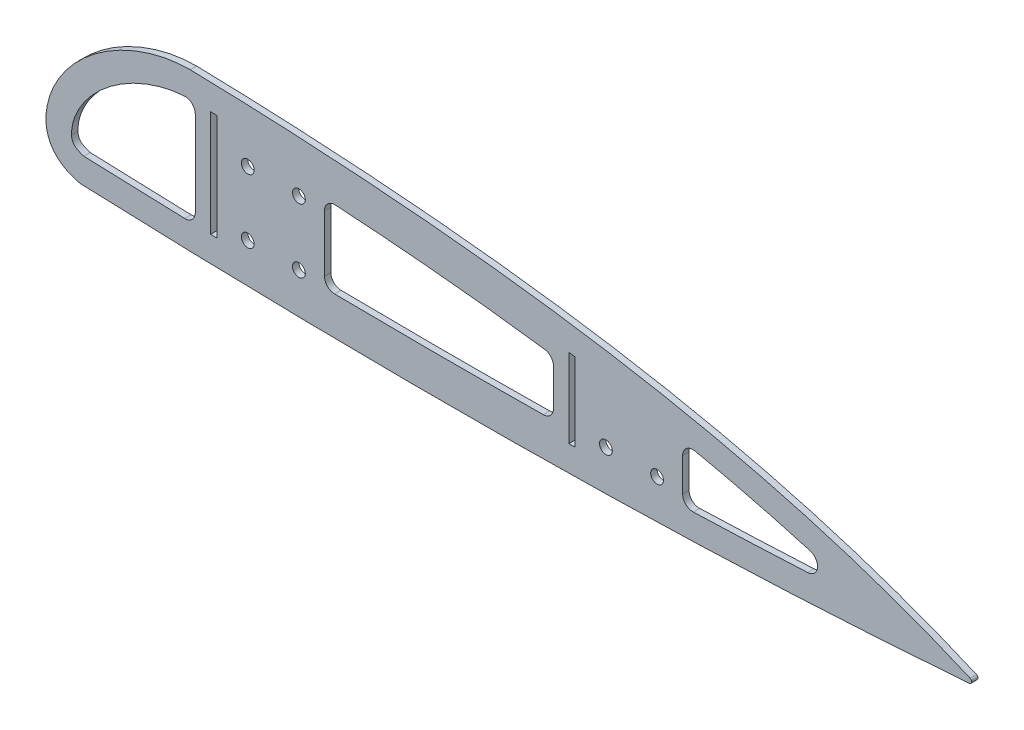
SolidWorks part; units mm, degrees
material "Balsa"
ref_plane "Front Plane" through (0, 0, 0) normal (0, 0, 1) x (1, 0, 0)
ref_plane "Top Plane" through (0, 0, 0) normal (0, 1, 0) x (1, 0, 0)
ref_plane "Right Plane" through (0, 0, 0) normal (1, 0, 0) x (0, 0, -1)
sketch "Sketch1" plane through (0, 0, 0) normal (0, 0, 1) x (1, 0, 0)
  line L0 (0, 0) -> (0, 277.8723) construction
  spline S0 degree 3 poles (-1817.1035, 43.2459) (-1814.9934, 43.2498) (-1812.9023, 43.1407) (-1808.752, 42.7311) (-1806.6929, 42.4302) (-1802.6035, 41.6561) (-1800.5732, 41.1827) (-1797.5481, 40.3507) (-1796.5432, 40.0529) (-1794.54, 39.4173) (-1793.5437, 39.0799) (-1788.6128, 37.3067) (-1784.805, 35.6079) (-1779.2882, 32.661) (-1777.4821, 31.6116) (-1774.8234, 29.9338) (-1773.9447, 29.3566) (-1772.2094, 28.1699) (-1771.3541, 27.5612) (-1768.8255, 25.689) (-1767.1896, 24.3793) (-1764.8142, 22.3175) (-1764.0355, 21.6139) (-1762.5056, 20.173) (-1761.7542, 19.4353) (-1759.5596, 17.1863) (-1758.1698, 15.6335) (-1755.5473, 12.4134) (-1754.3146, 10.7461) (-1752.0262, 7.2824) (-1750.9703, 5.4862) (-1749.5454, 2.676) (-1749.0957, 1.7161) (-1748.267, -0.2215) (-1747.8871, -1.2004) (-1746.8587, -4.1696) (-1746.3198, -6.1918) (-1745.7821, -9.3043) (-1745.6482, -10.3589) (-1745.4865, -12.47) (-1745.458, -13.528) (-1745.4874, -14.5886) knots 0 0 0 0 0.0625 0.0625 0.125 0.125 0.1875 0.1875 0.21875 0.21875 0.25 0.25 0.375 0.375 0.4375 0.4375 0.46875 0.46875 0.5 0.5 0.5625 0.5625 0.59375 0.59375 0.625 0.625 0.6875 0.6875 0.75 0.75 0.8125 0.8125 0.84375 0.84375 0.875 0.875 0.9375 0.9375 0.96875 0.96875 1 1 1 1
  spline S1 degree 3 poles (-1745.4874, -14.5886) (-1745.5191, -15.733) (-1745.6389, -16.8608) (-1745.9656, -18.5246) (-1746.0991, -19.0746) (-1746.4188, -20.1646) (-1746.6063, -20.7076) (-1747.2456, -22.2976) (-1747.7692, -23.2982) (-1748.699, -24.7111) (-1749.033, -25.1674) (-1749.7496, -26.0504) (-1750.1342, -26.479) (-1751.337, -27.6959) (-1752.2075, -28.4223) (-1753.6032, -29.4008) (-1754.0844, -29.7089) (-1755.0714, -30.2875) (-1755.573, -30.5556) (-1757.0993, -31.3032) (-1758.1455, -31.7263) (-1760.2858, -32.4471) (-1761.3799, -32.7445) (-1762.4949, -32.9869) knots 0 0 0 0 0.125 0.125 0.1875 0.1875 0.25 0.25 0.375 0.375 0.4375 0.4375 0.5 0.5 0.625 0.625 0.6875 0.6875 0.75 0.75 0.875 0.875 1 1 1 1
  spline S2 degree 3 poles (-1762.4949, -32.9869) (-1799.6912, -34.4623) (-1836.8983, -35.536) (-1892.7275, -36.4562) (-1911.3397, -36.6475) (-1948.5616, -36.7793) (-1967.1723, -36.72) (-2004.3932, -36.3278) (-2023.0051, -35.9948) (-2060.2115, -35.0301) (-2078.8075, -34.3983) (-2134.572, -32.0138) (-2171.7171, -29.7694) (-2208.8261, -26.7741) knots 0 0 0 0 0.25 0.25 0.375 0.375 0.5 0.5 0.625 0.625 0.75 0.75 1 1 1 1
  spline S3 degree 3 poles (-2208.8261, -26.7741) (-2193.5392, -19.9895) (-2178.0173, -13.8767) (-2146.5473, -2.869) (-2130.6, 2.0276) (-2110.436, 7.4917) (-2106.3936, 8.5512) (-2098.2976, 10.6045) (-2094.243, 11.5987) (-2082.06, 14.4883) (-2073.9125, 16.2908) (-2049.401, 21.3607) (-2032.9678, 24.2917) (-2008.204, 28.1331) (-1999.9354, 29.32) (-1983.39, 31.5219) (-1975.1103, 32.5374) (-1950.2526, 35.3512) (-1933.6558, 36.918) (-1900.4205, 39.5347) (-1883.7819, 40.5844) (-1850.4688, 42.2382) (-1833.7942, 42.8421) (-1817.1035, 43.2459) knots 0 0 0 0 0.125 0.125 0.25 0.25 0.28125 0.28125 0.3125 0.3125 0.375 0.375 0.5 0.5 0.5625 0.5625 0.625 0.625 0.75 0.75 0.875 0.875 1 1 1 1
  spline S4 degree 3 poles (2208.8261, -26.7741) (2193.5392, -19.9895) (2178.0173, -13.8767) (2146.5473, -2.869) (2130.6, 2.0276) (2110.436, 7.4917) (2106.3936, 8.5512) (2098.2976, 10.6045) (2094.243, 11.5987) (2082.06, 14.4883) (2073.9125, 16.2908) (2049.401, 21.3607) (2032.9678, 24.2917) (2008.204, 28.1331) (1999.9354, 29.32) (1983.39, 31.5219) (1975.1103, 32.5374) (1950.2526, 35.3512) (1933.6558, 36.918) (1900.4205, 39.5347) (1883.7819, 40.5844) (1850.4688, 42.2382) (1833.7942, 42.8421) (1817.1035, 43.2459) knots 0 0 0 0 0.125 0.125 0.25 0.25 0.28125 0.28125 0.3125 0.3125 0.375 0.375 0.5 0.5 0.5625 0.5625 0.625 0.625 0.75 0.75 0.875 0.875 1 1 1 1
  spline S5 degree 3 poles (1762.4949, -32.9869) (1799.6912, -34.4623) (1836.8983, -35.536) (1892.7275, -36.4562) (1911.3397, -36.6475) (1948.5616, -36.7793) (1967.1723, -36.72) (2004.3932, -36.3278) (2023.0051, -35.9948) (2060.2115, -35.0301) (2078.8075, -34.3983) (2134.572, -32.0138) (2171.7171, -29.7694) (2208.8261, -26.7741) knots 0 0 0 0 0.25 0.25 0.375 0.375 0.5 0.5 0.625 0.625 0.75 0.75 1 1 1 1
  spline S6 degree 3 poles (1745.4874, -14.5886) (1745.5191, -15.733) (1745.6389, -16.8608) (1745.9656, -18.5246) (1746.0991, -19.0746) (1746.4188, -20.1646) (1746.6063, -20.7076) (1747.2456, -22.2976) (1747.7692, -23.2982) (1748.699, -24.7111) (1749.033, -25.1674) (1749.7496, -26.0504) (1750.1342, -26.479) (1751.337, -27.6959) (1752.2075, -28.4223) (1753.6032, -29.4008) (1754.0844, -29.7089) (1755.0714, -30.2875) (1755.573, -30.5556) (1757.0993, -31.3032) (1758.1455, -31.7263) (1760.2858, -32.4471) (1761.3799, -32.7445) (1762.4949, -32.9869) knots 0 0 0 0 0.125 0.125 0.1875 0.1875 0.25 0.25 0.375 0.375 0.4375 0.4375 0.5 0.5 0.625 0.625 0.6875 0.6875 0.75 0.75 0.875 0.875 1 1 1 1
  spline S7 degree 3 poles (1817.1035, 43.2459) (1814.9934, 43.2498) (1812.9023, 43.1407) (1808.752, 42.7311) (1806.6929, 42.4302) (1802.6035, 41.6561) (1800.5732, 41.1827) (1797.5481, 40.3507) (1796.5432, 40.0529) (1794.54, 39.4173) (1793.5437, 39.0799) (1788.6128, 37.3067) (1784.805, 35.6079) (1779.2882, 32.661) (1777.4821, 31.6116) (1774.8234, 29.9338) (1773.9447, 29.3566) (1772.2094, 28.1699) (1771.3541, 27.5612) (1768.8255, 25.689) (1767.1896, 24.3793) (1764.8142, 22.3175) (1764.0355, 21.6139) (1762.5056, 20.173) (1761.7542, 19.4353) (1759.5596, 17.1863) (1758.1698, 15.6335) (1755.5473, 12.4134) (1754.3146, 10.7461) (1752.0262, 7.2824) (1750.9703, 5.4862) (1749.5454, 2.676) (1749.0957, 1.7161) (1748.267, -0.2215) (1747.8871, -1.2004) (1746.8587, -4.1696) (1746.3198, -6.1918) (1745.7821, -9.3043) (1745.6482, -10.3589) (1745.4865, -12.47) (1745.458, -13.528) (1745.4874, -14.5886) knots 0 0 0 0 0.0625 0.0625 0.125 0.125 0.1875 0.1875 0.21875 0.21875 0.25 0.25 0.375 0.375 0.4375 0.4375 0.46875 0.46875 0.5 0.5 0.5625 0.5625 0.59375 0.59375 0.625 0.625 0.6875 0.6875 0.75 0.75 0.8125 0.8125 0.84375 0.84375 0.875 0.875 0.9375 0.9375 0.96875 0.96875 1 1 1 1
  point P4 (0, 0)
extrude "Boss-Extrude1" add sketch "Sketch1" along normal blind 3.175 contours S4 S7 S6 S5
sketch "Sketch2" plane through (0, 0, 3.175) normal (0, 0, 1) x (1, 0, 0)
  line L0 (1828.8, 103.0782) -> (1828.8, -123.1482) construction
  line L1 (1830.3875, 30.1757) -> (1830.3875, -22.516)
  line L2 (1838.0075, -22.708) -> (1838.0075, 29.926)
  line L3 (1827.2125, 30.2712) -> (1827.2125, -22.4324)
  line L4 (1819.5925, -22.223) -> (1819.5925, 30.4801)
  line L5 (2006.6, 99.9892) -> (2006.6, -113.9514) construction
  line L6 (2008.1875, 15.2652) -> (2008.1875, -23.5191)
  line L7 (2015.8075, -23.3846) -> (2015.8075, 14.1011)
  line L8 (2005.0125, -23.5705) -> (2005.0125, 15.7343)
  line L9 (1997.3925, -23.6825) -> (1997.3925, 16.8229)
  spline S8 degree 3 poles (2652.6551, -883.4411) (2553.7866, -220.6936) (2326.648, -51.0111) (2062.8098, 5.6473) (2055.8756, 7.0487) (2041.9767, 9.6962) (2035.0159, 10.9415) (2014.1023, 14.4621) (2000.1185, 16.5232) (1979.0905, 19.2527) (1972.0724, 20.102) (1958.02, 21.6889) (1950.9843, 22.4269) (1929.8674, 24.4841) (1915.7768, 25.6475) (1887.5741, 27.6168) (1873.4618, 28.4216) (1513.5065, 44.9069) (1161.8936, -34.6274) (817.3447, 2.411) knots -2.073692 -2.073692 -2.073692 -2.073692 0.25 0.25 0.3125 0.3125 0.375 0.375 0.5 0.5 0.5625 0.5625 0.625 0.625 0.75 0.75 0.875 0.875 3.936157 3.936157 3.936157 3.936157 only from (2151.4898, -18.0926) to (1816.9464, 30.546)
  spline S9 degree 3 poles (3152.2547, -4780.3965) (2072.9924, -225.4169) (1912.8792, 40.4985) (1810.2893, 30.1168) (1808.6538, 29.8753) (1803.7889, 28.9562) (1800.6008, 28.0863) (1796.6764, 26.7151) (1795.8946, 26.4265) (1794.3371, 25.8209) (1793.5601, 25.5031) (1791.2529, 24.5129) (1789.7442, 23.8026) (1785.3024, 21.5278) (1782.4524, 19.8216) (1779.0358, 17.44) (1778.3599, 16.9511) (1777.0231, 15.9475) (1776.3613, 15.4319) (1774.4074, 13.8508) (1773.1498, 12.754) (1770.7294, 10.4705) (1769.5665, 9.284) (1767.3453, 6.8118) (1766.2867, 5.5264) (1764.79, 3.5118) (1764.3053, 2.8241) (1763.3753, 1.4252) (1762.9305, 0.7152) (1761.6627, -1.4496) (1760.9049, -2.9383) (1759.9339, -5.2578) (1759.6371, -6.0491) (1759.1156, -7.6456) (1758.8909, -8.4502) (1758.5253, -10.0745) (1758.3839, -10.8941) (1752.3074, -65.8609) (1959.4143, -158.0174) (6647.2205, -1049.5852) knots -3.757537 -3.757537 -3.757537 -3.757537 0.0625 0.0625 0.125 0.125 0.25 0.25 0.28125 0.28125 0.3125 0.3125 0.375 0.375 0.5 0.5 0.53125 0.53125 0.5625 0.5625 0.625 0.625 0.6875 0.6875 0.75 0.75 0.78125 0.78125 0.8125 0.8125 0.875 0.875 0.90625 0.90625 0.9375 0.9375 0.96875 0.96875 3.010971 3.010971 3.010971 3.010971 only from (1816.9464, 30.546) to (1758.1825, -14.2372)
  spline S10 degree 3 poles (-3166.0037, -873.8506) (1992.933, 99.0761) (1752.4316, 17.7876) (1758.3631, -15.7808) (1758.4624, -16.1562) (1758.686, -16.7046) (1758.7725, -16.8824) (1758.9676, -17.2203) (1759.0766, -17.3816) (1759.4361, -17.8433) (1759.7211, -18.1232) (1760.3263, -18.6169) (1760.6493, -18.8352) (1761.324, -19.2323) (1761.6761, -19.4105) (1806.3934, -39.4374) (1952.112, 205.9186) (114.7315, -4737.8807) knots -10.747112 -10.747112 -10.747112 -10.747112 0.125 0.125 0.25 0.25 0.3125 0.3125 0.375 0.375 0.5 0.5 0.625 0.625 0.75 0.75 16.284378 16.284378 16.284378 16.284378 only from (1758.1825, -14.2372) to (1764.2448, -20.3462)
  spline S11 degree 3 poles (-2634.7945, -1519.7839) (-1086.4185, 756.9354) (377.2087, 5.5874) (1893.3387, -23.8396) (1925.6248, -24.1253) (1974.0525, -23.9623) (1990.1967, -23.8092) (2022.4771, -23.2895) (2038.6136, -22.923) (3078.4011, 8.1349) (4085.7775, 504.0157) (4998.1231, 3716.244) knots -11.241889 -11.241889 -11.241889 -11.241889 0.25 0.25 0.5 0.5 0.625 0.625 0.75 0.75 8.681644 8.681644 8.681644 8.681644 only from (1764.2448, -20.3462) to (2151.4898, -18.0926)
  spline S12 degree 3 poles (2151.4898, -18.0926) (2124.6599, -9.0343) (2097.3625, -1.7728) (2062.8098, 5.6473) (2055.8756, 7.0487) (2041.9767, 9.6962) (2035.0159, 10.9415) (2014.1023, 14.4621) (2000.1185, 16.5232) (1979.0905, 19.2527) (1972.0724, 20.102) (1958.02, 21.6889) (1950.9843, 22.4269) (1929.8674, 24.4841) (1915.7768, 25.6475) (1887.5741, 27.6168) (1873.4618, 28.4216) (1845.2182, 29.7151) (1831.0867, 30.2029) (1816.9464, 30.546) knots 0 0 0 0 0.25 0.25 0.3125 0.3125 0.375 0.375 0.5 0.5 0.5625 0.5625 0.625 0.625 0.75 0.75 0.875 0.875 1 1 1 1
  spline S13 degree 3 poles (1816.9464, 30.546) (1815.2595, 30.5443) (1813.5922, 30.4511) (1810.2893, 30.1168) (1808.6538, 29.8753) (1803.7889, 28.9562) (1800.6008, 28.0863) (1796.6764, 26.7151) (1795.8946, 26.4265) (1794.3371, 25.8209) (1793.5601, 25.5031) (1791.2529, 24.5129) (1789.7442, 23.8026) (1785.3024, 21.5278) (1782.4524, 19.8216) (1779.0358, 17.44) (1778.3599, 16.9511) (1777.0231, 15.9475) (1776.3613, 15.4319) (1774.4074, 13.8508) (1773.1498, 12.754) (1770.7294, 10.4705) (1769.5665, 9.284) (1767.3453, 6.8118) (1766.2867, 5.5264) (1764.79, 3.5118) (1764.3053, 2.8241) (1763.3753, 1.4252) (1762.9305, 0.7152) (1761.6627, -1.4496) (1760.9049, -2.9383) (1759.9339, -5.2578) (1759.6371, -6.0491) (1759.1156, -7.6456) (1758.8909, -8.4502) (1758.5253, -10.0745) (1758.3839, -10.8941) (1758.2007, -12.5509) (1758.159, -13.3882) (1758.1825, -14.2372) knots 0 0 0 0 0.0625 0.0625 0.125 0.125 0.25 0.25 0.28125 0.28125 0.3125 0.3125 0.375 0.375 0.5 0.5 0.53125 0.53125 0.5625 0.5625 0.625 0.625 0.6875 0.6875 0.75 0.75 0.78125 0.78125 0.8125 0.8125 0.875 0.875 0.90625 0.90625 0.9375 0.9375 0.96875 0.96875 1 1 1 1
  spline S14 degree 3 poles (1758.1825, -14.2372) (1758.1934, -14.6298) (1758.2282, -15.0177) (1758.3631, -15.7808) (1758.4624, -16.1562) (1758.686, -16.7046) (1758.7725, -16.8824) (1758.9676, -17.2203) (1759.0766, -17.3816) (1759.4361, -17.8433) (1759.7211, -18.1232) (1760.3263, -18.6169) (1760.6493, -18.8352) (1761.324, -19.2323) (1761.6761, -19.4105) (1762.7469, -19.8901) (1763.4871, -20.1411) (1764.2448, -20.3462) knots 0 0 0 0 0.125 0.125 0.25 0.25 0.3125 0.3125 0.375 0.375 0.5 0.5 0.625 0.625 0.75 0.75 1 1 1 1
  spline S15 degree 3 poles (1764.2448, -20.3462) (1796.5071, -21.618) (1828.7779, -22.5865) (1893.3387, -23.8396) (1925.6248, -24.1253) (1974.0525, -23.9623) (1990.1967, -23.8092) (2022.4771, -23.2895) (2038.6136, -22.923) (2087.011, -21.4774) (2119.2597, -20.0514) (2151.4898, -18.0926) knots 0 0 0 0 0.25 0.25 0.5 0.5 0.625 0.625 0.75 0.75 1 1 1 1
  dimension "D2" = 3.175
  dimension "D3" = 1.5875
  dimension "D4" = 7.62
  dimension "D5" = 7.62
  dimension "D6" = 1828.8
  dimension "D7" = 3.175
  dimension "D8" = 1.5875
  dimension "D9" = 7.62
  dimension "D10" = 7.62
  dimension "D11" = 2006.6
  dimension "D1" = 12.7
extrude "Cut-Extrude1" cut sketch "Sketch2" against normal through all contours S14 S15 L4 S12 S13 | L2 S15 S12 | S12 L0 S15 L1 | L7 S15 S12 | L8 S15 L6 S12
sketch "Sketch3" plane through (0, 0, 0) normal (1, 0, 0) x (0, 0, -1)
  line L0 (60.199, 104.901) -> (165.1, 0)
  line L1 (165.1, 0) -> (60.199, -104.901)
  line L2 (0, 0) -> (0, -102.0924) construction
  dimension "D1" = 45
  dimension "D2" = 165.1
surface "Surface-Extrude1" sketch "Sketch3" parameters "D1"=2286
sketch "Sketch6" plane through (0, 0, 3.175) normal (0, 0, 1) x (1, 0, 0)
  line L0 (1838.0075, -22.708) -> (1838.0075, 29.926) construction
  line L1 (1838.0075, -22.708) -> (1838.0075, 29.926)
  line L2 (1723.1951, 3.175) -> (2177.9168, 3.175) construction
  line L3 (1723.1951, -3.175) -> (2197.3944, -3.175) construction
  line L4 (2015.8075, -23.3846) -> (2015.8075, 14.1011) construction
  line L5 (2015.8075, -23.3846) -> (2015.8075, 14.1011)
  line L6 (2061.5275, -22.2317) -> (2061.5275, 5.8821)
  line L7 (2061.5275, -22.2317) -> (2061.5275, -29.2718)
  line L8 (1883.7275, -23.5963) -> (1883.7275, 27.7896)
  line L9 (2061.5275, -29.2718) -> (2011.4629, -29.2718)
  line L10 (2011.4629, -29.2718) -> (2011.4629, 16.739)
  line L11 (2011.4629, 16.739) -> (2061.5275, 16.739)
  line L12 (2061.5275, 16.739) -> (2061.5275, 5.8821)
  line L13 (1996.5153, 10.5338) -> (1997.3925, 10.4115)
  line L14 (1997.3925, -23.6825) -> (1997.3925, 16.8229) construction
  line L15 (1997.3925, -23.6825) -> (1997.3925, 16.8229)
  line L16 (1997.3925, 16.8229) -> (1883.7275, -23.5963) construction
  line L17 (1997.3057, -17.3331) -> (1997.3925, -17.3319)
  circle A0 centre (1845.6275, 15.875) radius 3.175
  circle A1 centre (1871.0275, 15.875) radius 3.175
  circle A2 centre (1845.6275, -15.875) radius 3.175
  circle A3 centre (1871.0275, -15.875) radius 3.175
  circle A4 centre (2023.4275, -15.875) radius 3.175
  circle A5 centre (2048.8275, -15.875) radius 3.175
  spline S0 degree 3 poles (-1129.2707, -121.8954) (-120.4731, 340.5167) (865.7433, -3.8947) (1893.3387, -23.8396) (1925.6248, -24.1253) (2815.5262, -21.1305) (3677.6288, 260.6798) (3714.8587, 2000.1924) knots -7.250761 -7.250761 -7.250761 -7.250761 0.4576 0.4576 0.7076 0.7076 7.348551 7.348551 7.348551 7.348551 only from (1838.0075, -22.708) to (1997.3925, -23.6825) construction
  spline S1 degree 3 poles (3035.0392, -2650.7317) (2886.0553, -374.4761) (2455.6808, -42.6097) (1979.0905, 19.2527) (1972.0724, 20.102) (1958.02, 21.6889) (1950.9843, 22.4269) (1929.8674, 24.4841) (1915.7768, 25.6475) (1887.5741, 27.6168) (1873.4618, 28.4216) (1040.0019, 66.5926) (188.2244, -431.2077) (-525.2002, 1354.133) knots -4.091426 -4.091426 -4.091426 -4.091426 0.095667 0.095667 0.158167 0.158167 0.220667 0.220667 0.345667 0.345667 0.470667 0.470667 7.723066 7.723066 7.723066 7.723066 only from (1997.3925, 16.8229) to (1838.0075, 29.926) construction
  spline S2 degree 3 poles (1838.0075, -22.708) (1845.6906, -22.8954) (1853.3742, -23.0639) (1893.3387, -23.8396) (1925.6248, -24.1253) (1971.0708, -23.9724) (1984.2326, -23.8624) (1997.3925, -23.6825) knots 0.398089 0.398089 0.398089 0.398089 0.4576 0.4576 0.7076 0.7076 0.809511 0.809511 0.809511 0.809511
  spline S3 degree 3 poles (1997.3925, 16.8229) (1993.6309, 17.3476) (1989.8666, 17.854) (1979.0905, 19.2527) (1972.0724, 20.102) (1958.02, 21.6889) (1950.9843, 22.4269) (1929.8674, 24.4841) (1915.7768, 25.6475) (1887.5741, 27.6168) (1873.4618, 28.4216) (1852.2316, 29.3939) (1845.1207, 29.6792) (1838.0075, 29.926) knots 0.06208 0.06208 0.06208 0.06208 0.095667 0.095667 0.158167 0.158167 0.220667 0.220667 0.345667 0.345667 0.470667 0.470667 0.533587 0.533587 0.533587 0.533587
  spline S4 degree 3 poles (-794.4197, -681.0876) (127.7606, 325.7089) (1098.3427, -51.0084) (2831.6651, 0.765) (3599.2072, 292.0002) (4322.943, 1835.3892) knots -7.310004 -7.310004 -7.310004 -7.310004 0.10055 0.10055 6.120396 6.120396 6.120396 6.120396 only from (2015.8075, -23.3846) to (2151.4898, -18.0926) construction
  spline S5 degree 3 poles (2657.5865, -2880.9528) (2834.2246, -487.0141) (2492.2566, -86.575) (2062.8098, 5.6473) (2055.8756, 7.0487) (2041.9767, 9.6962) (2035.0159, 10.9415) (1433.9632, 112.1237) (764.7415, -307.0817) (518.88, 2199.1021) knots -2.983019 -2.983019 -2.983019 -2.983019 0.838461 0.838461 0.900961 0.900961 0.963461 0.963461 6.289681 6.289681 6.289681 6.289681 only from (2151.4898, -18.0926) to (2015.8075, 14.1011) construction
  spline S6 degree 3 poles (2015.8075, -23.3846) (2028.7895, -23.1417) (2041.7691, -22.8287) (2087.011, -21.4774) (2119.2597, -20.0514) (2151.4898, -18.0926) knots 0 0 0 0 0.10055 0.10055 0.35055 0.35055 0.35055 0.35055
  spline S7 degree 3 poles (2151.4898, -18.0926) (2124.6599, -9.0343) (2097.3625, -1.7728) (2062.8098, 5.6473) (2055.8756, 7.0487) (2041.9767, 9.6962) (2035.0159, 10.9415) (2023.9691, 12.8011) (2019.89, 13.4628) (2015.8075, 14.1011) knots 0.588461 0.588461 0.588461 0.588461 0.838461 0.838461 0.900961 0.900961 0.963461 0.963461 1 1 1 1
  spline S8 degree 1 poles (1996.5153, 10.5338) (1837.7873, 23.5798) knots 0 0 1 1 construction
  spline S9 degree 3 poles (1996.5153, 10.5338) (1983.3769, 12.3663) (1957.0483, 15.5829) (1917.3628, 19.2596) (1877.6206, 21.9292) (1851.0656, 23.1191) (1837.7873, 23.5798) knots 0.06208 0.06208 0.06208 0.06208 0.179956 0.297833 0.41571 0.533587 0.533587 0.533587 0.533587
  spline S10 degree 1 poles (1838.1623, -16.3599) (1997.3057, -17.3331) knots 0 0 1 1 construction
  spline S11 degree 3 poles (1838.1623, -16.3599) (1851.4231, -16.6833) (1877.9485, -17.2178) (1917.737, -17.6649) (1957.5238, -17.7346) (1984.0456, -17.5144) (1997.3057, -17.3331) knots 0.398089 0.398089 0.398089 0.398089 0.500945 0.6038 0.706656 0.809511 0.809511 0.809511 0.809511
  dimension "D3" = 6.35
  dimension "D1" = 27.0962
  dimension "D2" = 6.35
  dimension "D4" = 12.7
  dimension "D5" = 12.7
  dimension "D6" = 7.62
  dimension "D7" = 25.4
  dimension "D8" = 12.7
  dimension "D9" = 12.7
  dimension "D10" = 7.62
  dimension "D11" = 25.4
  dimension "D12" = 6.35
extrude "Boss-Extrude7" add sketch "Sketch6" against normal up to surface (3.175 mm away)
fillet "Fillet1" radius 5.08 9 edges at (1997.3925, -17.3319, 1.5875) (1997.3925, 10.4115, 1.5875) (1883.7275, 21.4284, 1.5875) (1883.7275, -17.2456, 1.5875)
fillet "Fillet2" radius 1.27 1 edges at (2208.8261, -26.7741, 1.5875)
equation "\"D5@Sketch6\"=\"D4@Sketch6\""
equation "\"D9@Sketch6\"=\"D8@Sketch6\""
equation "\"D10@Sketch6\"=\"D6@Sketch6\""
equation "\"D11@Sketch6\"=\"D7@Sketch6\""
